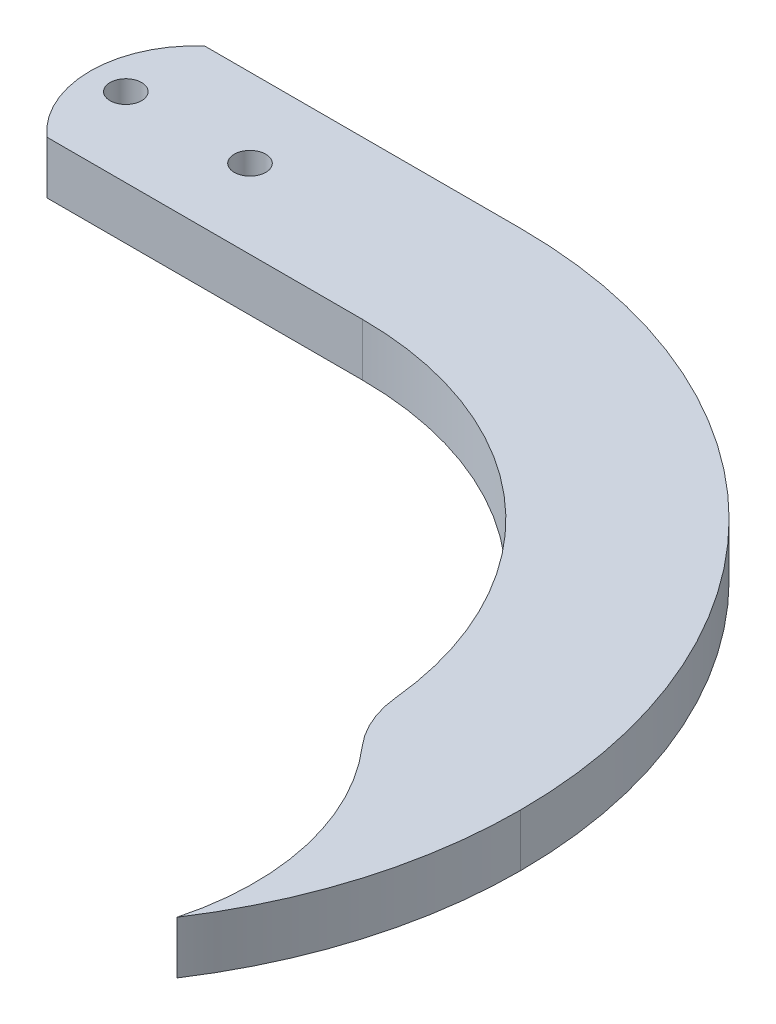
SolidWorks part; units mm, degrees
ref_plane "Front" through (0, 0, 0) normal (0, 0, 1) x (1, 0, 0)
ref_plane "Top" through (0, 0, 0) normal (0, 1, 0) x (1, 0, 0)
ref_plane "Right" through (0, 0, 0) normal (1, 0, 0) x (0, 0, -1)
sketch "Sketch1" plane through (0, 0, 0) normal (0, 1, 0) x (1, 0, 0)
  line L0 (0, 0) -> (30, 0) construction
  line L1 (0, 7.5) -> (30, 7.5)
  line L2 (0, -7.5) -> (30, -7.5)
  line L3 (62.875, -40.375) -> (77.875, -40.375) construction
  arc A0 (0, 7.5) -> (0, -7.5) centre (0, 0) ccw
  arc A5 (30, -7.5) -> (30, 7.5) centre (30, 0) ccw
  arc A6 (30, 0) -> (70.375, -40.375) centre (30, -40.375) cw construction
  arc A7 (77.875, -40.375) -> (30, 7.5) centre (30, -40.375) ccw
  arc A8 (62.875, -40.375) -> (30, -7.5) centre (30, -40.375) ccw
  arc A9 (62.875, -40.375) -> (77.875, -40.375) centre (70.375, -40.375) ccw
  arc A10 (30, 7.5) -> (30, -7.5) centre (30, 0) ccw
  circle A11 centre (0, 0) radius 1.5
  circle A12 centre (11.8, 0) radius 1.5
  point P2 (15, 0)
  point P12 (58.5494, -11.8256)
  dimension "D1" = 30
  dimension "D2" = 7.5
  dimension "D3" = 32.875
  dimension "D4" = 11.8
  dimension "D5" = 3
extrude "Boss-Extrude1" add sketch "Sketch1" along normal blind 5 contours A10 L1 A0 L2 A12 A11 | A5 A10 | A8 A9 A7 A5
sketch "Sketch2" plane through (0, 5, 0) normal (0, 1, 0) x (1, 0, 0)
  arc A0 (0, 7.5) -> (0, -7.5) centre (0, 0) ccw construction
  arc A1 (0, 7.5) -> (0, -7.5) centre (0, 0) ccw
  arc A2 (0, 7.5) -> (0, -7.5) centre (6.6144, 0) ccw
  dimension "D1" = 10
extrude "Cut-Extrude1" cut sketch "Sketch2" against normal blind 10 contours A1 A2
sketch "Sketch3" plane through (0, 5, 0) normal (0, 1, 0) x (1, 0, 0)
  arc A0 (62.875, -40.375) -> (77.875, -40.375) centre (70.375, -40.375) ccw construction
  arc A1 (68.4826, -47.6323) -> (77.875, -40.375) centre (70.375, -40.375) ccw
  arc A2 (77.875, -40.375) -> (70.375, -65.5194) centre (31.9756, -40.375) cw
  arc A3 (62.875, -40.375) -> (70.375, -65.5194) centre (46.2319, -59.03) cw
  arc M7 (62.875, -40.375) -> (77.875, -40.375) centre (70.375, -40.375) ccw
  dimension "D1" = 25
extrude "Boss-Extrude2" add sketch "Sketch3" against normal up to surface (5 mm away) contours A3 A2 M7
sketch "Sketch4" plane through (0, 5, 0) normal (0, 1, 0) x (1, 0, 0)
  arc A0 (68.4826, -47.6323) -> (77.875, -40.375) centre (70.375, -40.375) ccw construction
  arc A1 (70.375, -65.5194) -> (77.875, -40.375) centre (31.9756, -40.375) ccw construction
  arc A2 (70.375, -65.5194) -> (62.875, -40.375) centre (46.2319, -59.03) ccw construction
  arc A3 (68.4826, -47.6323) -> (77.875, -40.375) centre (70.375, -40.375) ccw
  arc A4 (70.375, -65.5194) -> (77.875, -40.375) centre (31.9756, -40.375) ccw
  arc A5 (70.375, -65.5194) -> (62.875, -40.375) centre (46.2319, -59.03) ccw
  arc A6 (62.875, -40.375) -> (68.4826, -47.6323) centre (70.375, -40.375) ccw construction
  arc A7 (62.875, -40.375) -> (68.4826, -47.6323) centre (70.375, -40.375) ccw
  arc M7 (62.875, -40.375) -> (68.4826, -47.6323) centre (70.375, -40.375) ccw
extrude "Cut-Extrude2" cut sketch "Sketch4" against normal blind 10 contours A5 M7
fillet "Fillet1" radius 10 1 edges at (62.875, 2.5, 40.375)
